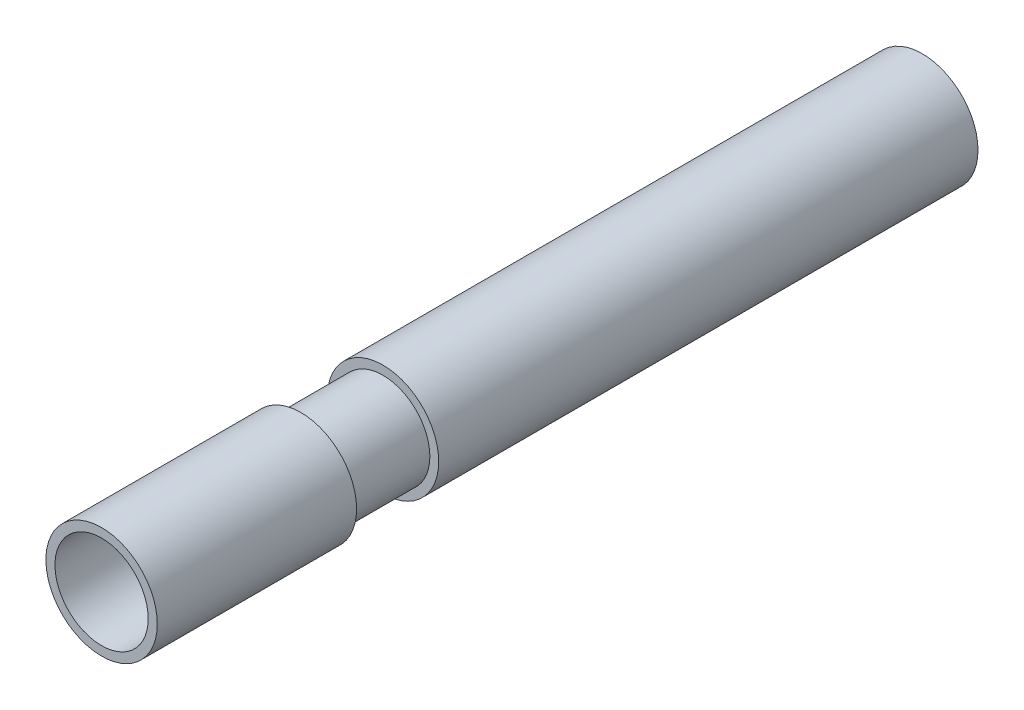
SolidWorks part; units mm, degrees
other "Markup1"
sketch "Sketch6"
material "Brass"
ref_plane "Front Plane" through (0, 0, 0) normal (0, 0, 1) x (1, 0, 0)
ref_plane "Top Plane" through (0, 0, 0) normal (0, 1, 0) x (1, 0, 0)
ref_plane "Right Plane" through (0, 0, 0) normal (1, 0, 0) x (0, 0, -1)
sketch "Sketch1" plane through (0, 0, 0) normal (1, 0, 0) x (0, 0, -1)
  line L0 (0, 0) -> (35.56, 0) construction
  line L1 (0, 0) -> (0, 2.413)
  line L2 (0, 2.413) -> (8.636, 2.413)
  line L3 (8.636, 2.413) -> (8.636, 2.032)
  line L4 (8.636, 2.032) -> (12.192, 2.032)
  line L5 (12.192, 2.032) -> (12.192, 2.413)
  line L6 (12.192, 2.413) -> (35.56, 2.413)
  line L7 (35.56, 2.413) -> (35.56, 0)
  line L8 (35.56, 0) -> (0, 0)
  dimension "D1" = 2.413
  dimension "D2" = 35.56
  dimension "D3" = 0.381
  dimension "D4" = 3.556
  dimension "D5" = 8.636
revolve "Revolve1" add sketch "Sketch1" angle 360 about L0
ref_plane "Plane1" through (0, 0, 0) normal (0, 0, 1) x (1, 0, 0)
sketch "Sketch2" plane through (0, 0, 0) normal (0, 0, 1) x (1, 0, 0)
  circle A0 centre (0, 0) radius 2.0193
  dimension "D1" = 4.0386
extrude "Cut-Extrude2" cut sketch "Sketch2" against normal through all
ref_plane "Plane3" through (0, 0, -30.48) normal (0, 0, -1) x (-1, 0, 0)
sketch "Sketch10" plane through (0, 0, -30.48) normal (0, 0, -1) x (-1, 0, 0)
  circle A0 centre (0, 0) radius 2.0193 construction
  circle A1 centre (0, 0) radius 2.0193
curve "Helix/Spiral1" pitch 0.5292 height 3.7042 turns 7
sketch "Sketch12" plane through (0, 0, -30.48) normal (0, 0, -1) x (-1, 0, 0)
  line L1 (-1.726, 0) -> (-2.1659, 0.254)
  line L2 (-2.1659, 0.254) -> (-2.1659, -0.254)
  line L3 (-2.1659, -0.254) -> (-1.726, 0)
  circle A0 centre (-2.0193, 0) radius 0.1466 construction
  dimension "D1" = 0.254
sweep "Cut-Sweep1" cut profiles "Sketch12" path "Helix/Spiral1"
